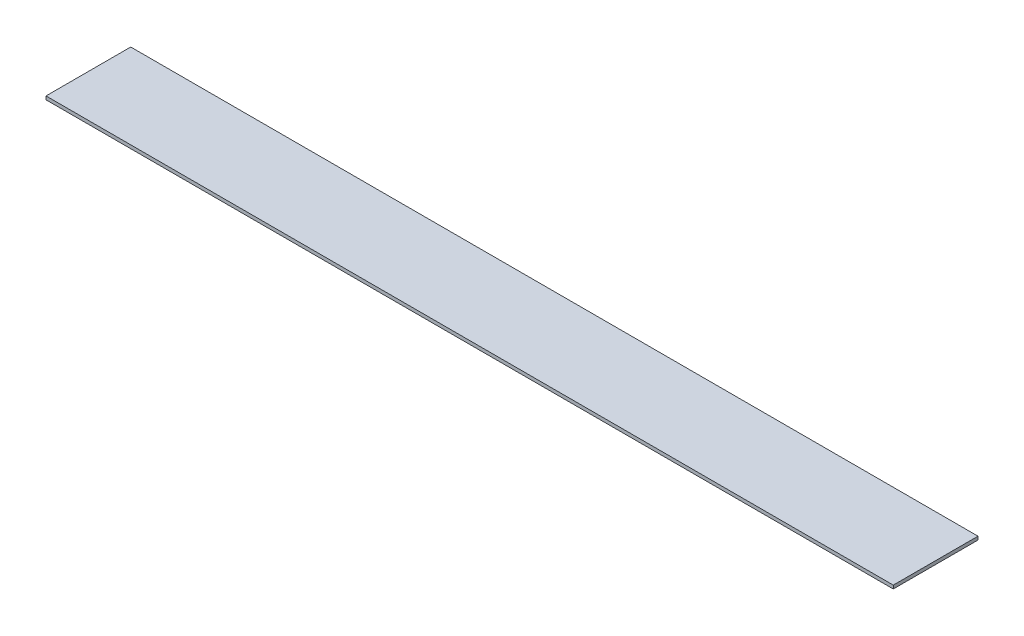
SolidWorks part; units mm, degrees
ref_plane "Front Plane" through (0, 0, 0) normal (0, 0, 1) x (1, 0, 0)
ref_plane "Top Plane" through (0, 0, 0) normal (0, 1, 0) x (1, 0, 0)
ref_plane "Right Plane" through (0, 0, 0) normal (1, 0, 0) x (0, 0, -1)
sketch "Sketch1" plane through (0, 0, 0) normal (0, 1, 0) x (1, 0, 0)
  line L0 (0, 0) -> (250, 0)
  line L1 (0, 0) -> (0, 25)
  line L2 (250, 0) -> (250, 25)
  line L3 (0, 25) -> (250, 25)
  dimension "D1" = 25
  dimension "D2" = 250
extrude "Boss-Extrude1" add sketch "Sketch1" along normal blind 1
